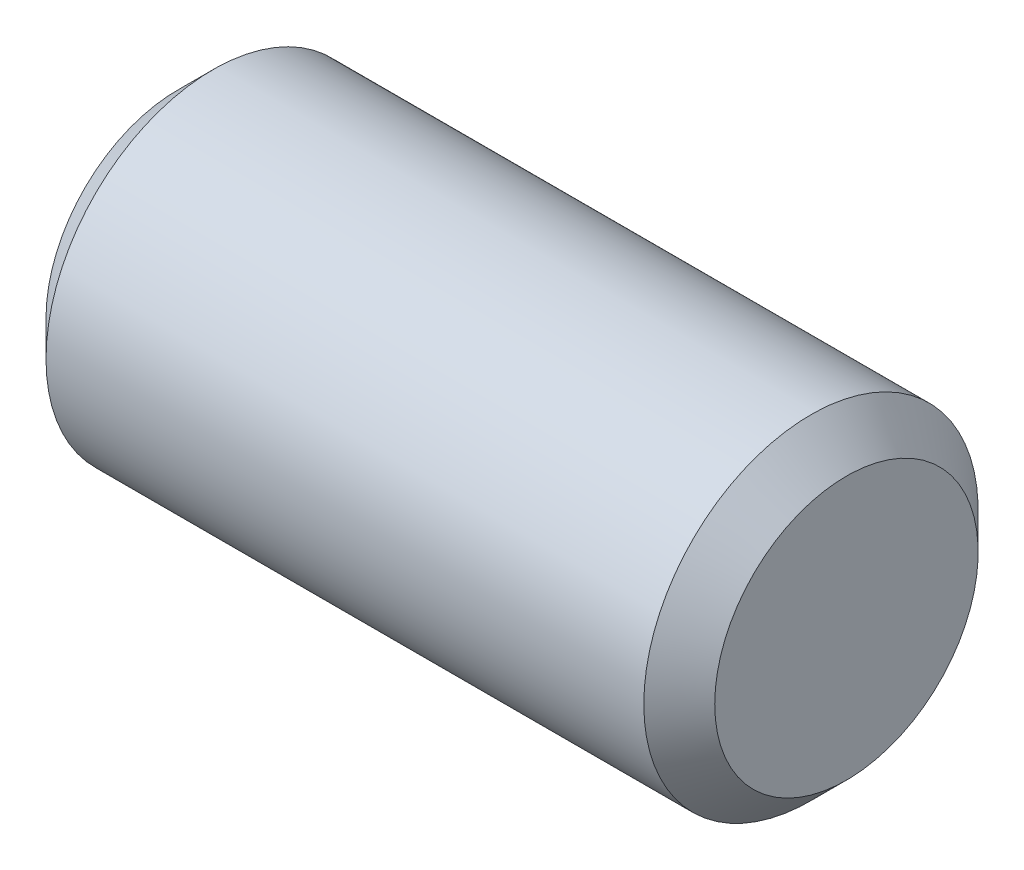
SolidWorks part; units mm, degrees
ref_plane "Front Plane" through (0, 0, 0) normal (0, 0, 1) x (1, 0, 0)
ref_plane "Top Plane" through (0, 0, 0) normal (0, 1, 0) x (1, 0, 0)
ref_plane "Right Plane" through (0, 0, 0) normal (1, 0, 0) x (0, 0, -1)
sketch "Sketch1" plane through (0, 0, 0) normal (0, 0, 1) x (1, 0, 0)
  line L0 (-3.0074, 0) -> (3.0074, 0) construction
  line L1 (-1.8066, 0) -> (-1.8066, -0.7879)
  line L2 (-1.5945, -1) -> (1.9813, -1)
  line L3 (2.1934, -0.7879) -> (2.1934, 0)
  line L4 (2.1934, -0.7879) -> (1.9813, -1)
  line L6 (-1.8066, -0.7879) -> (-1.5945, -1)
  line L7 (-1.8066, 0) -> (2.1934, 0)
  point P4 (0, 0)
  dimension "D2" = 45
  dimension "D3" = 0.3
revolve "Revolve1" add sketch "Sketch1" angle 360 about L0
